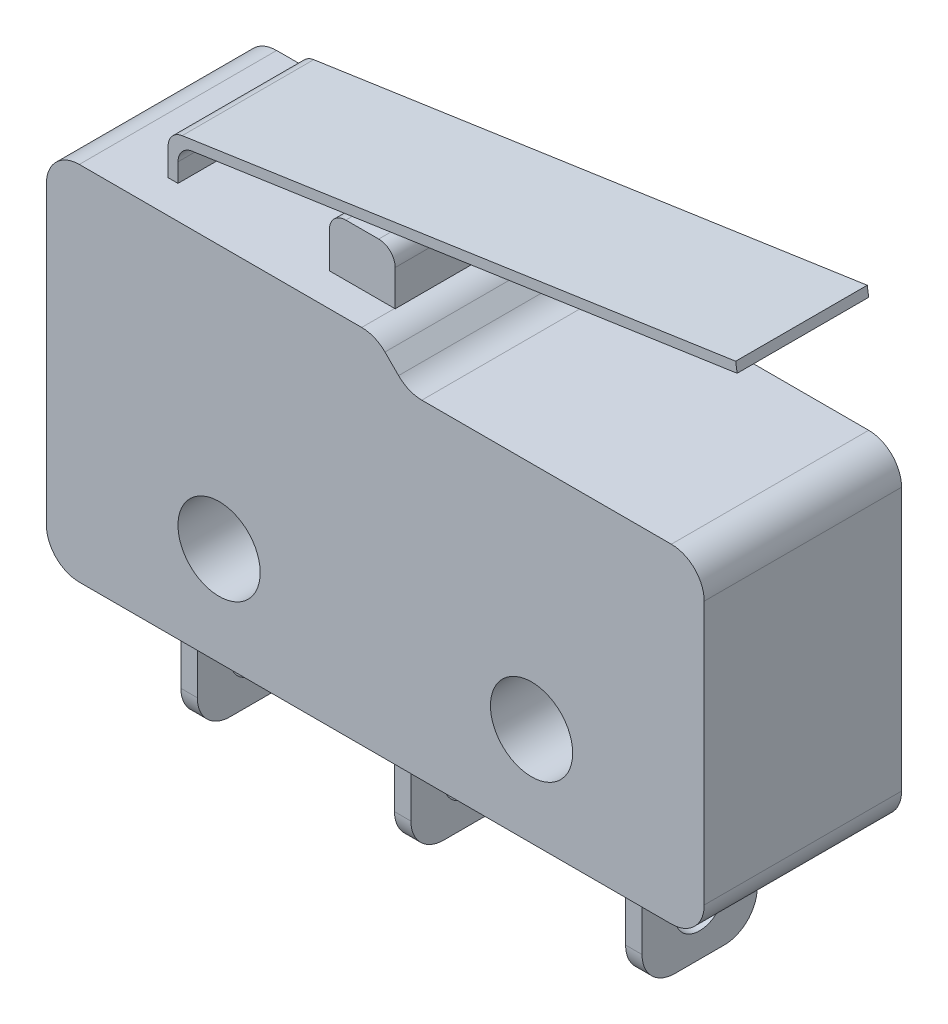
SolidWorks part; units mm, degrees
ref_plane "Front Plane" through (0, 0, 0) normal (0, 0, 1) x (1, 0, 0)
ref_plane "Top Plane" through (0, 0, 0) normal (0, 1, 0) x (1, 0, 0)
ref_plane "Right Plane" through (0, 0, 0) normal (1, 0, 0) x (0, 0, -1)
ref_plane "Plane1" through (0, 0, 1) normal (0, 0, -1) x (-1, 0, 0)
sketch "Sketch1" plane through (0, 0, 1) normal (0, 0, -1) x (-1, 0, 0)
  line L0 (4.7433, 8.0828) -> (4.0361, 7.3757)
  line L1 (4.0361, 7.3757) -> (12.3361, 7.3757)
  line L2 (12.3361, 7.3757) -> (12.3361, 9.6348)
  line L3 (12.3361, 9.6348) -> (12.0798, 9.6725)
  line L4 (12.0798, 9.6725) -> (12.0361, 9.3757)
  line L5 (12.0361, 9.3757) -> (12.0361, 8.3757)
  line L6 (12.0361, 8.3757) -> (5.4504, 8.3757)
  arc A0 (5.4504, 8.3757) -> (4.7433, 8.0828) centre (5.4504, 7.3757) ccw
extrude "Boss-Extrude1" add sketch "Sketch1" against normal blind 4
sketch "Sketch2" plane through (0, 0, 5) normal (0, 0, 1) x (1, 0, 0)
  line L0 (-12.3361, 7.3757) -> (-12.3361, 9.6348)
  line L1 (-12.3361, 9.6348) -> (-12.0798, 9.6725)
  line L2 (-12.0798, 9.6725) -> (-12.0361, 9.3757)
  line L3 (-12.0361, 9.3757) -> (-12.0361, 8.3757)
  line L4 (-12.0361, 8.3757) -> (-5.4504, 8.3757)
  line L5 (-4.7433, 8.0828) -> (-4.0361, 7.3757)
  line L6 (-4.0361, 7.3757) -> (-12.3361, 7.3757)
  arc A0 (-5.4504, 8.3757) -> (-4.7433, 8.0828) centre (-5.4504, 7.3757) cw
extrude "Boss-Extrude2" add sketch "Sketch2" along normal blind 1
sketch "Sketch3" plane through (0, 0, 6) normal (0, 0, 1) x (1, 0, 0)
  line L0 (-12.0361, 8.3757) -> (-12.0361, 9.3757)
  line L1 (-12.0361, 9.3757) -> (-12.0798, 9.6725)
  line L2 (-12.0798, 9.6725) -> (-12.3361, 9.6348)
  line L3 (-12.3361, 9.6348) -> (-12.3361, 8.3757)
  line L4 (-12.3361, 8.3757) -> (-12.0361, 8.3757)
extrude "Cut-Extrude1" cut sketch "Sketch3" against normal blind 1
sketch "Sketch4" plane through (0, 7.3757, 0) normal (0, -1, 0) x (1, 0, 0)
  line L0 (-4.0361, 1) -> (-12.3361, 1)
  line L1 (-12.3361, 1) -> (-12.3361, 6)
  line L2 (-12.3361, 6) -> (-4.0361, 6)
  line L3 (-4.0361, 6) -> (-4.0361, 1)
extrude "Boss-Extrude3" add sketch "Sketch4" along normal blind 10
sketch "Sketch5" plane through (-10.4318, -1.5341, 0) normal (0.9894, 0.1455, 0) x (0, 0, -1)
  line L0 (-1, 11.3271) -> (-1, 11.0271)
  line L1 (-1, 11.0271) -> (-5, 11.0271)
  line L2 (-5, 11.0271) -> (-5, 11.3271)
  line L3 (-5, 11.3271) -> (-1, 11.3271)
extrude "Boss-Extrude4" add sketch "Sketch5" along normal blind 17.1828
sketch "Sketch6" plane through (-4.0361, 0, 0) normal (1, 0, 0) x (0, 0, -1)
  line L0 (-1, 7.3757) -> (-1, -2.6243)
  line L1 (-1, -2.6243) -> (-6, -2.6243)
  line L2 (-6, -2.6243) -> (-6, 7.3757)
  line L3 (-6, 7.3757) -> (-1, 7.3757)
extrude "Boss-Extrude5" add sketch "Sketch6" along normal blind 9
sketch "Sketch7" plane through (-12.3361, 0, 0) normal (-1, 0, 0) x (0, 0, 1)
  line L0 (1, -2.6243) -> (1, 8.3757)
  line L1 (1, 8.3757) -> (6, 8.3757)
  line L2 (6, 8.3757) -> (6, -2.6243)
  line L3 (6, -2.6243) -> (1, -2.6243)
extrude "Boss-Extrude6" add sketch "Sketch7" along normal blind 2.7
sketch "Sketch8" plane through (0, 0, 1) normal (0, 0, -1) x (-1, 0, 0)
  line L0 (15.0361, 8.3757) -> (15.0361, -2.6243)
  line L1 (15.0361, -2.6243) -> (-4.9639, -2.6243)
  line L2 (-4.9639, -2.6243) -> (-4.9639, 7.3757)
  line L3 (-4.9639, 7.3757) -> (4.0361, 7.3757)
  line L4 (4.0361, 7.3757) -> (4.7433, 8.0828)
  line L5 (5.4504, 8.3757) -> (15.0361, 8.3757)
  arc A0 (4.7433, 8.0828) -> (5.4504, 8.3757) centre (5.4504, 7.3757) cw
extrude "Boss-Extrude7" add sketch "Sketch8" along normal blind 1
sketch "Sketch9" plane through (0, 8.3757, 0) normal (0, 1, 0) x (-1, 0, 0)
  line L0 (7.4326, 1) -> (5.4326, 1)
  line L1 (5.4326, 1) -> (5.4326, 5)
  line L2 (5.4326, 5) -> (7.4326, 5)
  line L3 (7.4326, 5) -> (7.4326, 1)
extrude "Boss-Extrude8" add sketch "Sketch9" along normal blind 1.5866
sketch "Sketch10" plane through (0, -2.6243, 0) normal (0, -1, 0) x (1, 0, 0)
  line L0 (-5.7035, 4.75) -> (-5.2035, 4.75)
  line L1 (-5.2035, 4.75) -> (-5.2035, 1.25)
  line L2 (-5.2035, 1.25) -> (-5.7035, 1.25)
  line L3 (-5.7035, 1.25) -> (-5.7035, 4.75)
extrude "Boss-Extrude9" add sketch "Sketch10" along normal blind 3.5
sketch "Sketch11" plane through (0, -2.6243, 0) normal (0, -1, 0) x (1, 0, 0)
  line L0 (1.3227, 4.75) -> (1.8227, 4.75)
  line L1 (1.8227, 4.75) -> (1.8227, 1.25)
  line L2 (1.8227, 1.25) -> (1.3227, 1.25)
  line L3 (1.3227, 1.25) -> (1.3227, 4.75)
extrude "Boss-Extrude10" add sketch "Sketch11" along normal blind 3.5
sketch "Sketch12" plane through (0, -2.6243, 0) normal (0, -1, 0) x (1, 0, 0)
  line L0 (-12.1987, 4.75) -> (-11.6987, 4.75)
  line L1 (-11.6987, 4.75) -> (-11.6987, 1.25)
  line L2 (-11.6987, 1.25) -> (-12.1987, 1.25)
  line L3 (-12.1987, 1.25) -> (-12.1987, 4.75)
extrude "Boss-Extrude11" add sketch "Sketch12" along normal blind 3.5
hole_wizard "Ø2.5 (2.5) Diameter Hole1" positions "Sketch14" profile "Sketch13" hole size "Ø2.5" standard "ANSI Metric"
sketch "Sketch14" plane through (0, 0, 6) normal (0, 0, 1) x (1, 0, 0)
  point P0 (-9.7861, 0.3757)
  point P1 (-0.2861, 0.3757)
sketch "Sketch13" plane through (-9.7861, 0.3757, 6) normal (1, 0, 0) x (0, -1, 0)
  line L0 (0, 0) -> (0, 6)
  line L1 (0, 6) -> (1.25, 6)
  line L2 (1.25, 6) -> (1.25, 0)
  line L5 (1.25, 0) -> (0, 0)
  line L11 (0, -6.35) -> (0, 107.95) construction
  dimension "Thru Hole Dia." = 2.5
  dimension "Thru Hole Depth" = 6
hole_wizard "Ø1.5 (1.5) Diameter Hole1" positions "Sketch16" profile "Sketch15" hole size "Ø1.5" standard "ANSI Metric"
sketch "Sketch16" plane through (-11.6987, 0, 0) normal (1, 0, 0) x (0, 0, -1)
  point P0 (-3, -4.6243)
sketch "Sketch15" plane through (-11.6987, -4.6243, 3) normal (0, 1, 0) x (0, 0, -1)
  line L0 (0, 0) -> (0, 3.3375)
  line L1 (0, 3.3375) -> (0.75, 3.3375)
  line L2 (0.75, 3.3375) -> (0.75, 0)
  line L5 (0.75, 0) -> (0, 0)
  line L11 (0, -6.35) -> (0, 107.95) construction
  dimension "Thru Hole Dia." = 1.5
  dimension "Thru Hole Depth" = 3.3375
hole_wizard "Ø1.5 (1.5) Diameter Hole2" positions "Sketch18" profile "Sketch17" hole size "Ø1.5" standard "ANSI Metric"
sketch "Sketch18" plane through (1.3227, 0, 0) normal (-1, 0, 0) x (0, 0, 1)
  point P0 (3, -4.6243)
sketch "Sketch17" plane through (1.3227, -4.6243, 3) normal (0, 1, 0) x (0, 0, 1)
  line L0 (0, 0) -> (0, 3.6412)
  line L1 (0, 3.6412) -> (0.75, 3.6412)
  line L2 (0.75, 3.6412) -> (0.75, 0)
  line L5 (0.75, 0) -> (0, 0)
  line L11 (0, -6.35) -> (0, 107.95) construction
  dimension "Thru Hole Dia." = 1.5
  dimension "Thru Hole Depth" = 3.6412
hole_wizard "Ø1.5 (1.5) Diameter Hole3" positions "Sketch20" profile "Sketch19" hole size "Ø1.5" standard "ANSI Metric"
sketch "Sketch20" plane through (-5.7035, 0, 0) normal (-1, 0, 0) x (0, 0, 1)
  point P0 (3, -4.6243)
sketch "Sketch19" plane through (-5.7035, -4.6243, 3) normal (0, 1, 0) x (0, 0, 1)
  line L0 (0, 0) -> (0, 10.6674)
  line L1 (0, 10.6674) -> (0.75, 10.6674)
  line L2 (0.75, 10.6674) -> (0.75, 0)
  line L5 (0.75, 0) -> (0, 0)
  line L11 (0, -6.35) -> (0, 107.95) construction
  dimension "Thru Hole Dia." = 1.5
  dimension "Thru Hole Depth" = 10.6674
fillet "Fillet1" radius 0.5 4 edges at (-5.4326, 9.9623, 3) (-12.3361, 9.6348, 3) (-7.4326, 9.9623, 3) (-12.0361, 9.3757, 3)
fillet "Fillet2" radius 1 11 edges at (4.9639, -2.6243, 3) (-15.0361, 8.3757, 3) (-4.0361, 7.3757, 3) (-11.9487, -6.1243, 4.75) (-5.4535, -6.1243, 4.75) (4.9639, 7.3757, 3) (-5.4535, -6.1243, 1.25) (-15.0361, -2.6243, 3) (1.5727, -6.1243, 4.75) (1.5727, -6.1243, 1.25) (-11.9487, -6.1243, 1.25)
